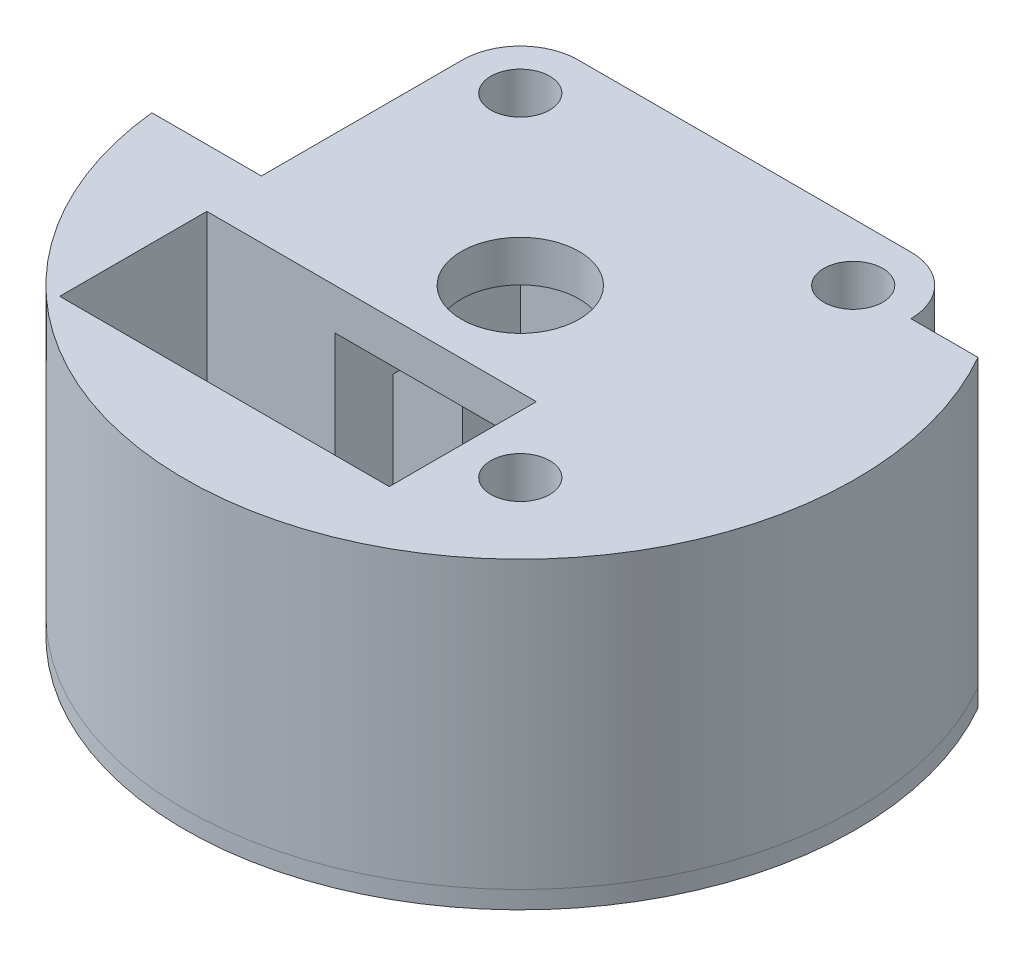
SolidWorks part; units mm, degrees
ref_plane "Front Plane" through (0, 0, 0) normal (0, 0, 1) x (1, 0, 0)
ref_plane "Top Plane" through (0, 0, 0) normal (0, 1, 0) x (1, 0, 0)
ref_plane "Right Plane" through (0, 0, 0) normal (1, 0, 0) x (0, 0, -1)
sketch "Sketch2" plane through (0, 0, 0) normal (0, 1, 0) x (1, 0, 0)
  line L0 (-24.1835, 17.9605) -> (-24.1835, 3.75)
  line L1 (-17.9605, 17.9605) -> (17.9605, 17.9605) construction
  line L2 (-17.9605, 17.9605) -> (-17.9605, -17.9605) construction
  line L3 (-17.9605, -17.9605) -> (17.9605, -17.9605) construction
  line L4 (17.9605, 17.9605) -> (17.9605, -17.9605) construction
  line L5 (-17.9605, 17.9605) -> (17.9605, -17.9605) construction
  line L6 (-17.9605, -17.9605) -> (17.9605, 17.9605) construction
  line L7 (30, -10) -> (11.7375, -10)
  line L8 (30, -10) -> (30, 10)
  line L9 (30, 10) -> (-10, 10)
  line L10 (-10, -10) -> (-10, -3.75)
  line L11 (30, -10) -> (-10, 10) construction
  line L12 (30, 10) -> (-10, -10) construction
  line L13 (-24.1835, -3.75) -> (-10, -3.75)
  line L14 (-24.1835, -3.75) -> (-24.1835, 3.75) construction
  line L15 (-24.1835, 3.75) -> (-10, 3.75)
  line L16 (-10, 0) -> (-10, 3.75) construction
  line L17 (-24.1835, -3.75) -> (-10, 3.75) construction
  line L18 (-24.1835, 3.75) -> (-10, -3.75) construction
  line L19 (11.7375, -25.875) -> (-23.8225, -25.875) construction
  line L20 (11.7375, -11.7375) -> (11.7375, -10) construction
  line L21 (-17.9605, -10) -> (-23.8225, -10) construction
  line L22 (-23.8225, -25.875) -> (-23.8225, -10) construction
  line L23 (11.7375, -25.875) -> (-23.8225, -10) construction
  line L24 (11.7375, -10) -> (-23.8225, -25.875) construction
  line L25 (-24.1835, -3.75) -> (-36.0002, -3.75)
  line L26 (-17.9605, 24.1835) -> (17.9605, 24.1835)
  line L27 (24.1835, 17.9605) -> (31.4245, 17.9605)
  line L28 (-10, -3.75) -> (-10, 0) construction
  line L29 (-10, 3.75) -> (-10, 10)
  line L30 (-10, -3.75) -> (-10, 0) construction
  line L31 (-10, 0) -> (-10, 3.75) construction
  line L32 (11.7375, -10) -> (10, -10)
  line L33 (0, -10) -> (-10, -10)
  line L34 (11.7375, -10) -> (10, -10) construction
  line L35 (10, -10) -> (0, -10)
  line L36 (10, -10) -> (0, -10) construction
  line L37 (0, -10) -> (-10, -10) construction
  line L38 (11.7375, -25.875) -> (11.7375, -17.9605) construction
  line L39 (11.7375, -17.9605) -> (11.7375, -11.7375) construction
  line L40 (-10, -10) -> (-17.9605, -10) construction
  circle A0 centre (0, 0) radius 10 construction
  circle A1 centre (-17.9605, 17.9605) radius 3.175
  circle A2 centre (17.9605, 17.9605) radius 3.175
  circle A3 centre (17.9605, -17.9605) radius 3.175
  circle A4 centre (-17.9605, -17.9605) radius 3.175 construction
  arc A5 (-36.0002, -3.75) -> (31.4245, 17.9605) centre (0, 0) ccw
  arc A6 (13.5602, -13.5602) -> (11.7375, -17.9605) centre (17.9605, -17.9605) ccw construction
  arc A7 (-17.9605, 24.1835) -> (-24.1835, 17.9605) centre (-17.9605, 17.9605) ccw
  arc A8 (24.1835, 17.9605) -> (17.9605, 24.1835) centre (17.9605, 17.9605) ccw
  arc A9 (31.4245, 17.9605) -> (-36.0002, -3.75) centre (0, 0) ccw construction
  arc A10 (11.7375, 17.9605) -> (13.5602, 13.5602) centre (17.9605, 17.9605) ccw construction
  arc A11 (17.9605, 24.1835) -> (11.7375, 17.9605) centre (17.9605, 17.9605) ccw construction
  arc A12 (13.5602, 13.5602) -> (17.9605, 11.7375) centre (17.9605, 17.9605) ccw construction
  arc A13 (17.9605, 11.7375) -> (24.1835, 17.9605) centre (17.9605, 17.9605) ccw construction
  arc A14 (-24.1835, 17.9605) -> (-17.9605, 11.7375) centre (-17.9605, 17.9605) ccw construction
  arc A15 (-17.9605, 11.7375) -> (-13.5602, 13.5602) centre (-17.9605, 17.9605) ccw construction
  arc A16 (-13.5602, 13.5602) -> (-11.7375, 17.9605) centre (-17.9605, 17.9605) ccw construction
  arc A17 (-11.7375, 17.9605) -> (-17.9605, 24.1835) centre (-17.9605, 17.9605) ccw construction
  arc A18 (11.7375, -17.9605) -> (17.9605, -11.7375) centre (17.9605, -17.9605) ccw construction
  arc A19 (17.9605, -11.7375) -> (13.5602, -13.5602) centre (17.9605, -17.9605) ccw construction
  point P11 (10, 0)
  point P17 (-17.0918, 0)
  point P23 (-6.0425, -17.9375)
  dimension "D1" = 6.35
  dimension "D3" = 20
  dimension "D5" = 72.39
  dimension "D2" = 50.8
  dimension "D4" = 40
  dimension "D6" = 7.5
  dimension "D7" = 35.56
  dimension "D8" = 15.875
  dimension "D9" = 3.048
extrude "Boss-Extrude1" add sketch "Sketch2" along normal blind 1.905
sketch "Sketch3" plane through (0, 1.905, 0) normal (0, 1, 0) x (1, 0, 0)
  line L0 (-23.8225, -25.875) -> (-23.8225, -10) construction
  line L1 (-17.9605, -10) -> (-23.8225, -10) construction
  line L2 (-10, -10) -> (-17.9605, -10) construction
  line L3 (11.7375, -11.7375) -> (11.7375, -10) construction
  line L4 (11.7375, -17.9605) -> (11.7375, -11.7375) construction
  line L5 (11.7375, -25.875) -> (11.7375, -17.9605) construction
  line L6 (11.7375, -25.875) -> (-23.8225, -25.875) construction
  line L7 (-23.8225, -25.875) -> (-23.8225, -10)
  line L8 (-17.9605, -10) -> (-23.8225, -10)
  line L9 (-10, -10) -> (-17.9605, -10)
  line L10 (-10, 3.75) -> (-10, 10)
  line L11 (-10, 10) -> (30, 10)
  line L12 (30, 10) -> (30, -10)
  line L13 (30, -10) -> (-10, -10)
  line L14 (-10, -10) -> (-10, -3.75)
  line L15 (-10, -3.75) -> (-36.0002, -3.75)
  line L16 (31.4245, 17.9605) -> (24.1835, 17.9605)
  line L17 (17.9605, 24.1835) -> (-17.9605, 24.1835)
  line L18 (-24.1835, 17.9605) -> (-24.1835, 3.75)
  line L19 (-24.1835, 3.75) -> (-10, 3.75)
  line L20 (-10, 3.75) -> (-10, 10)
  line L21 (-10, 10) -> (30, 10)
  line L22 (30, 10) -> (30, -10)
  line L23 (30, -10) -> (11.7375, -10)
  line L24 (-10, -10) -> (-10, -3.75)
  line L25 (-10, -3.75) -> (-36.0002, -3.75)
  line L26 (31.4245, 17.9605) -> (24.1835, 17.9605)
  line L27 (17.9605, 24.1835) -> (-17.9605, 24.1835)
  line L28 (-24.1835, 17.9605) -> (-24.1835, 3.75)
  line L29 (-24.1835, 3.75) -> (-10, 3.75)
  line L30 (11.7375, -11.7375) -> (11.7375, -10)
  line L31 (11.7375, -17.9605) -> (11.7375, -11.7375)
  line L32 (11.7375, -25.875) -> (11.7375, -17.9605)
  line L33 (11.7375, -25.875) -> (-23.8225, -25.875)
  line L34 (11.7375, -10) -> (-10, -10) construction
  circle A0 centre (17.9605, 17.9605) radius 3.175 construction
  circle A1 centre (17.9605, -17.9605) radius 3.175 construction
  circle A2 centre (-17.9605, 17.9605) radius 3.175 construction
  arc A3 (-36.0002, -3.75) -> (31.4245, 17.9605) centre (0, 0) ccw
  arc A4 (24.1835, 17.9605) -> (17.9605, 24.1835) centre (17.9605, 17.9605) ccw
  arc A5 (-17.9605, 24.1835) -> (-24.1835, 17.9605) centre (-17.9605, 17.9605) ccw
  arc A6 (-36.0002, -3.75) -> (31.4245, 17.9605) centre (0, 0) ccw
  arc A7 (24.1835, 17.9605) -> (17.9605, 24.1835) centre (17.9605, 17.9605) ccw
  arc A8 (-17.9605, 24.1835) -> (-24.1835, 17.9605) centre (-17.9605, 17.9605) ccw
  circle A9 centre (17.9605, -17.9605) radius 3.175
  circle A10 centre (-17.9605, 17.9605) radius 3.175
  circle A11 centre (17.9605, 17.9605) radius 3.175
  dimension "D1" = 0
extrude "Boss-Extrude2" add sketch "Sketch3" along normal blind 19.431 separate body
sketch "Sketch4" plane through (0, 21.336, 0) normal (0, 1, 0) x (1, 0, 0)
  line L0 (-10, -3.75) -> (-10, 0) construction
  line L1 (-10, 0) -> (-10, 3.75) construction
  line L2 (-24.1835, -3.75) -> (-24.1835, 3.75) construction
  line L3 (-10, -3.75) -> (-10, 0)
  line L4 (-10, 0) -> (-10, 3.75)
  line L5 (-24.1835, -3.75) -> (-24.1835, 3.75)
  line L6 (-10, -3.75) -> (-24.1835, -3.75) construction
  line L14 (-24.1835, 3.75) -> (-10, 3.75)
  line L15 (-10, 3.75) -> (-10, 10)
  line L16 (-10, 10) -> (30, 10)
  line L17 (30, 10) -> (30, -10)
  line L18 (30, -10) -> (11.7375, -10)
  line L19 (11.7375, -10) -> (11.7375, -25.875)
  line L20 (11.7375, -25.875) -> (-23.8225, -25.875)
  line L21 (-23.8225, -25.875) -> (-23.8225, -10)
  line L22 (-23.8225, -10) -> (-10, -10)
  line L23 (-10, -10) -> (-10, -3.75)
  line L24 (-10, -3.75) -> (-36.0002, -3.75)
  line L25 (31.4245, 17.9605) -> (24.1835, 17.9605)
  line L26 (17.9605, 24.1835) -> (-17.9605, 24.1835)
  line L27 (-24.1835, 17.9605) -> (-24.1835, 3.75)
  line L28 (-24.1835, 3.75) -> (-10, 3.75) construction
  line L29 (-10, 3.75) -> (-10, 10)
  line L30 (-10, 10) -> (30, 10)
  line L31 (30, 10) -> (30, -10)
  line L32 (30, -10) -> (11.7375, -10)
  line L33 (11.7375, -10) -> (11.7375, -25.875)
  line L34 (11.7375, -25.875) -> (-23.8225, -25.875)
  line L35 (-23.8225, -25.875) -> (-23.8225, -10)
  line L36 (-23.8225, -10) -> (-10, -10)
  line L37 (-10, -10) -> (-10, -3.75)
  line L38 (-24.1835, -3.75) -> (-36.0002, -3.75)
  line L39 (31.4245, 17.9605) -> (24.1835, 17.9605)
  line L40 (17.9605, 24.1835) -> (-17.9605, 24.1835)
  line L41 (-24.1835, 17.9605) -> (-24.1835, 3.75)
  circle A2 centre (17.9605, -17.9605) radius 3.175 construction
  arc A3 (-36.0002, -3.75) -> (31.4245, 17.9605) centre (0, 0) ccw
  arc A4 (24.1835, 17.9605) -> (17.9605, 24.1835) centre (17.9605, 17.9605) ccw
  arc A5 (-17.9605, 24.1835) -> (-24.1835, 17.9605) centre (-17.9605, 17.9605) ccw
  arc A6 (-36.0002, -3.75) -> (31.4245, 17.9605) centre (0, 0) ccw
  arc A7 (24.1835, 17.9605) -> (17.9605, 24.1835) centre (17.9605, 17.9605) ccw
  arc A8 (-17.9605, 24.1835) -> (-24.1835, 17.9605) centre (-17.9605, 17.9605) ccw
  circle A9 centre (17.9605, -17.9605) radius 3.175
  circle A10 centre (17.9605, 17.9605) radius 3.175 construction
  circle A11 centre (17.9605, 17.9605) radius 3.175
  circle A12 centre (-17.9605, 17.9605) radius 3.175 construction
  circle A13 centre (-17.9605, 17.9605) radius 3.175
  dimension "D1" = 0
extrude "Boss-Extrude3" add sketch "Sketch4" along normal blind 6.985
sketch "Sketch5" plane through (0, 28.321, 0) normal (0, 1, 0) x (1, 0, 0)
  line L0 (11.7375, -25.875) -> (-23.8225, -25.875) construction
  line L1 (11.7375, -25.875) -> (11.7375, -17.9605) construction
  line L2 (11.7375, -11.7375) -> (11.7375, -10) construction
  line L3 (11.7375, -17.9605) -> (11.7375, -11.7375) construction
  line L4 (-24.1835, 17.9605) -> (-24.1835, -3.75)
  line L5 (-24.1835, -3.75) -> (-36.0002, -3.75)
  line L6 (31.4245, 17.9605) -> (24.1835, 17.9605)
  line L7 (17.9605, 24.1835) -> (-17.9605, 24.1835)
  line L8 (-24.1835, 17.9605) -> (-24.1835, -3.75)
  line L9 (-24.1835, -3.75) -> (-36.0002, -3.75)
  line L10 (31.4245, 17.9605) -> (24.1835, 17.9605)
  line L11 (17.9605, 24.1835) -> (-17.9605, 24.1835)
  line L12 (11.7375, -10) -> (10, -10) construction
  line L13 (10, -10) -> (0, -10) construction
  line L14 (0, -10) -> (-10, -10) construction
  line L15 (-10, -10) -> (-17.9605, -10) construction
  line L16 (-17.9605, -10) -> (-23.8225, -10) construction
  line L17 (-23.8225, -25.875) -> (-23.8225, -10) construction
  line L18 (11.7375, -25.875) -> (-23.8225, -25.875)
  line L19 (11.7375, -25.875) -> (11.7375, -17.9605)
  line L20 (11.7375, -11.7375) -> (11.7375, -10)
  line L21 (11.7375, -17.9605) -> (11.7375, -11.7375)
  line L22 (11.7375, -10) -> (10, -10)
  line L23 (10, -10) -> (0, -10)
  line L24 (0, -10) -> (-10, -10)
  line L25 (-10, -10) -> (-17.9605, -10)
  line L26 (-17.9605, -10) -> (-23.8225, -10)
  line L27 (-23.8225, -25.875) -> (-23.8225, -10)
  circle A0 centre (0, 0) radius 6.35
  circle A1 centre (17.9605, -17.9605) radius 3.175 construction
  circle A2 centre (17.9605, 17.9605) radius 3.175 construction
  arc A3 (-36.0002, -3.75) -> (31.4245, 17.9605) centre (0, 0) ccw
  arc A4 (24.1835, 17.9605) -> (17.9605, 24.1835) centre (17.9605, 17.9605) ccw
  arc A5 (-17.9605, 24.1835) -> (-24.1835, 17.9605) centre (-17.9605, 17.9605) ccw
  arc A6 (-36.0002, -3.75) -> (31.4245, 17.9605) centre (0, 0) ccw
  arc A7 (24.1835, 17.9605) -> (17.9605, 24.1835) centre (17.9605, 17.9605) ccw
  arc A8 (-17.9605, 24.1835) -> (-24.1835, 17.9605) centre (-17.9605, 17.9605) ccw
  circle A9 centre (-17.9605, 17.9605) radius 3.175 construction
  circle A10 centre (17.9605, -17.9605) radius 3.175
  circle A11 centre (17.9605, 17.9605) radius 3.175
  circle A12 centre (-17.9605, 17.9605) radius 3.175
  dimension "D2" = 12.7
  dimension "D1" = 0
extrude "Boss-Extrude4" add sketch "Sketch5" along normal blind 4.445
sketch "Sketch6" plane through (0, 0, -24.1835) normal (0, 0, -1) x (-1, 0, 0)
  line L1 (-13.335, 29.1085) -> (13.335, 29.1085) construction
  line L2 (-13.335, 29.1085) -> (-13.335, 11.3285) construction
  line L3 (-13.335, 11.3285) -> (13.335, 11.3285) construction
  line L4 (13.335, 29.1085) -> (13.335, 11.3285) construction
  line L5 (-13.335, 29.1085) -> (13.335, 11.3285) construction
  line L6 (-13.335, 11.3285) -> (13.335, 29.1085) construction
  line L7 (-10.9855, 12.7255) -> (10.9855, 12.7255) construction
  line L8 (-10.9855, 12.7255) -> (-10.9855, 27.7115) construction
  line L9 (-10.9855, 27.7115) -> (10.9855, 27.7115) construction
  line L10 (10.9855, 12.7255) -> (10.9855, 27.7115) construction
  line L11 (-10.9855, 12.7255) -> (10.9855, 27.7115) construction
  line L12 (-10.9855, 27.7115) -> (10.9855, 12.7255) construction
  circle A0 centre (-10.9855, 27.7115) radius 1.95
  circle A1 centre (10.9855, 27.7115) radius 1.95
  circle A2 centre (10.9855, 12.7255) radius 1.95
  circle A3 centre (-10.9855, 12.7255) radius 1.95
  point P0 (0, 20.2185)
  point P5 (0, 20.2185)
  dimension "D6" = 3.9
  dimension "D1" = 26.67
  dimension "D2" = 17.78
  dimension "D3" = 20.2185
  dimension "D4" = 21.971
  dimension "D5" = 14.986
extrude "Cut-Extrude1" cut sketch "Sketch6" against normal blind 5.7 and the other way through all
equation "\"AIRFRAME_OD\"= 3.142in"
equation "\"AIRFRAME_ID\"= 3.00in"
equation "\"FLAT_T\"= 0.125in"
equation "\"NOSE_EXP_L\"= 3.5in"
equation "\"NOSE_SHOULDER_L\"= 1.5in"
equation "\"MAIN_L\"= 30in"
equation "\"RECO_COUP_L\"= 6in"
equation "\"RECO_SWITCH_L\"= 1.5in"
equation "\"DROGUE_L\"= 14in"
equation "\"ATS_FORE_COUP_L\"= 4in"
equation "\"ATS_AFT_COUP_L\"= 2.5in"
equation "\"LOWER_L\"= 16in"
equation "\"FIN_N\"= 4"
equation "\"CR_AFT_X\"= 0.5in"
equation "\"CR_FORE_X\"= 6in"
equation "\"COUPLER_OD\"= 2.998in"
equation "\"COUPLER_ID\"= 2.875in"
equation "\"RECO_ROD_X\"= 1.5in"
equation "\"ATS_ROD_X\"= 2in"
equation "\"FIN_ROOT\"= 5in"
equation "\"FIN_X\"= 0.75in"
equation "\"MOTOR_OD\"= 2.25in"
equation "\"MOTOR_ID\"= 2.126in"
equation "\"MOTOR_L\"= 8in"
equation "\"MOTOR_LOWER_X\"= 0.5in"
equation "\"NOSE_CONE_L\"=14.5in"
equation "\"ATS_LIPO_L\" = 2.8in"
equation "\"ATS_LIPO_W\" = 0.625in"
equation "\"ATS_LIPO_H\" = 1.4in "
equation "\"ATS_STANDOFF_H\" = 10mm"
equation "\"ATS_STANDOFF_OD\" = 5.2mm"
equation "\"ATS_PCB_L\" = 2.5in"
equation "\"ATS_PCB_W\" = 1.45in"
equation "\"ATS_PCB_H\" = 1.2in"
equation "\"ATS_PCB_HOLESEP_W\" = 1.33in - 0.0985in"
equation "\"ATS_ALTI_L\" = 1.05in"
equation "\"ATS_ALTI_W\" = 0.7in"
equation "\"ATS_ALTI_H\" = 0.4in"
equation "\"D5@Sketch2\"=2.85in"
equation "\"D7@Sketch2\"=\"ATS_LIPO_H\""
equation "\"D8@Sketch2\"=\"ATS_LIPO_W\""
equation "\"D1@Sketch6\"=\"ATS_ALTI_L\""
equation "\"D2@Sketch6\"=\"ATS_ALTI_W\""
